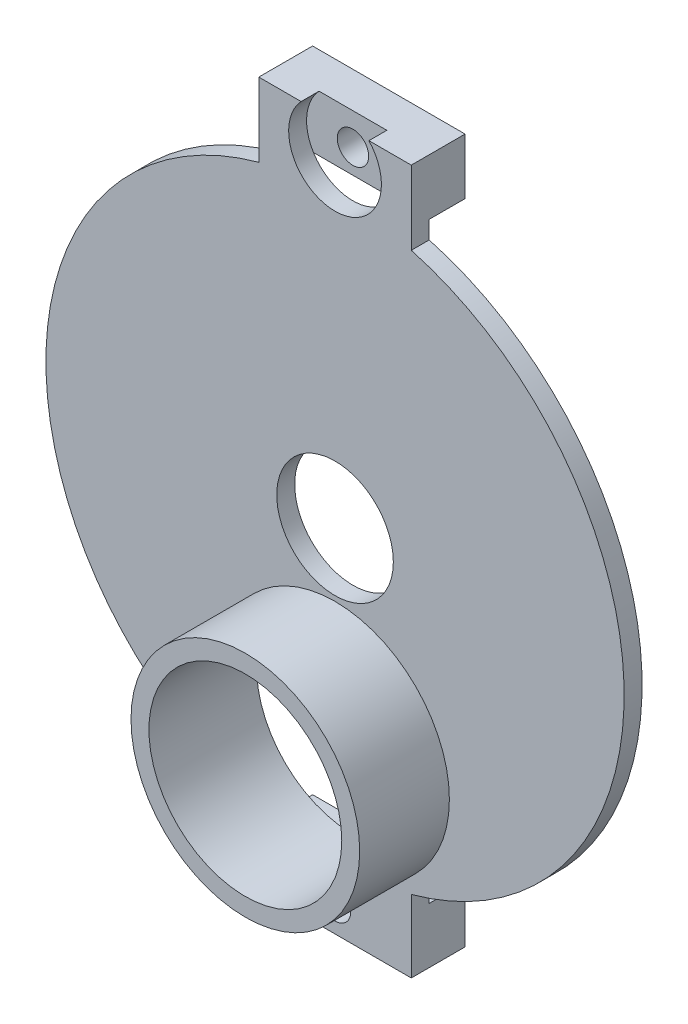
SolidWorks part; units mm, degrees
ref_plane "前视基准面" through (0, 0, 0) normal (0, 0, 1) x (1, 0, 0)
ref_plane "上视基准面" through (0, 0, 0) normal (0, 1, 0) x (1, 0, 0)
ref_plane "右视基准面" through (0, 0, 0) normal (1, 0, 0) x (0, 0, -1)
sketch "草图1" plane through (0, 0, 0) normal (0, 0, 1) x (1, 0, 0)
  line L0 (-8.5, -174.722) -> (-8.5, -191.7642) construction
  line L1 (-8.5, -113.2718) -> (8.5, -113.2718)
  line L2 (-8.5, -113.2718) -> (-8.5, -119.5097)
  line L3 (-8.5, -119.5097) -> (8.5, -119.5097)
  line L4 (8.5, -113.2718) -> (8.5, -119.5097)
  line L5 (8.5, -191.7642) -> (-8.5, -191.7642)
  line L6 (8.5, -191.7642) -> (8.5, -185.5636)
  line L7 (8.5, -185.5636) -> (-8.5, -185.5636)
  line L8 (-8.5, -191.7642) -> (-8.5, -185.5636)
  circle A0 centre (0, -188.7642) radius 1.75
  circle A1 centre (0, -116.8024) radius 1.75
extrude "凸台-拉伸1" add sketch "草图1" along normal blind 4
sketch "草图3" plane through (0, 0, 4) normal (0, 0, 1) x (1, 0, 0)
  line L1 (-8.5, -113.2718) -> (8.5, -113.2718)
  line L2 (-8.5, -113.2718) -> (-8.5, -121.5009)
  line L3 (-8.5, -191.7642) -> (8.5, -191.7642) construction
  line L4 (8.5, -113.2718) -> (8.5, -121.5009)
  line L5 (8.5, -191.7642) -> (-8.5, -191.7642)
  line L6 (8.5, -191.7642) -> (8.5, -183.6927)
  line L7 (8.5, -113.2718) -> (-8.5, -113.2718) construction
  line L8 (-8.5, -191.7642) -> (-8.5, -183.6927)
  arc A0 (8.5, -183.6927) -> (8.5, -121.5009) centre (0, -152.5968) ccw
  circle A1 centre (0, -172.3997) radius 10.75
  arc A2 (-8.5, -121.5009) -> (-8.5, -183.6927) centre (0, -152.5968) ccw
  circle A3 centre (0, -188.7642) radius 1.75 construction
  circle A4 centre (0, -116.8024) radius 1.75 construction
  circle A5 centre (0, -188.7642) radius 1.75
  circle A6 centre (0, -116.8024) radius 1.75
  dimension "D1" = 21.5
extrude "凸台-拉伸3" add sketch "草图3" along normal blind 2
sketch "草图4" plane through (0, 0, 6) normal (0, 0, 1) x (1, 0, 0)
  circle A0 centre (0, -152.5968) radius 6.5
  dimension "D1" = 13
extrude "切除-拉伸1" cut sketch "草图4" against normal blind 10
sketch "草图5" plane through (0, 0, 6) normal (0, 0, 1) x (1, 0, 0)
  circle A0 centre (0, -172.3997) radius 10.75 construction
  circle A1 centre (0, -172.3997) radius 10.75
extrude "拉伸-薄壁1" add sketch "草图5" along normal blind 10 thin
sketch "草图6" plane through (0, 0, 6) normal (0, 0, 1) x (1, 0, 0)
  circle A0 centre (0, -116.8024) radius 5.1716
extrude "切除-拉伸2" cut sketch "草图6" against normal blind 2
